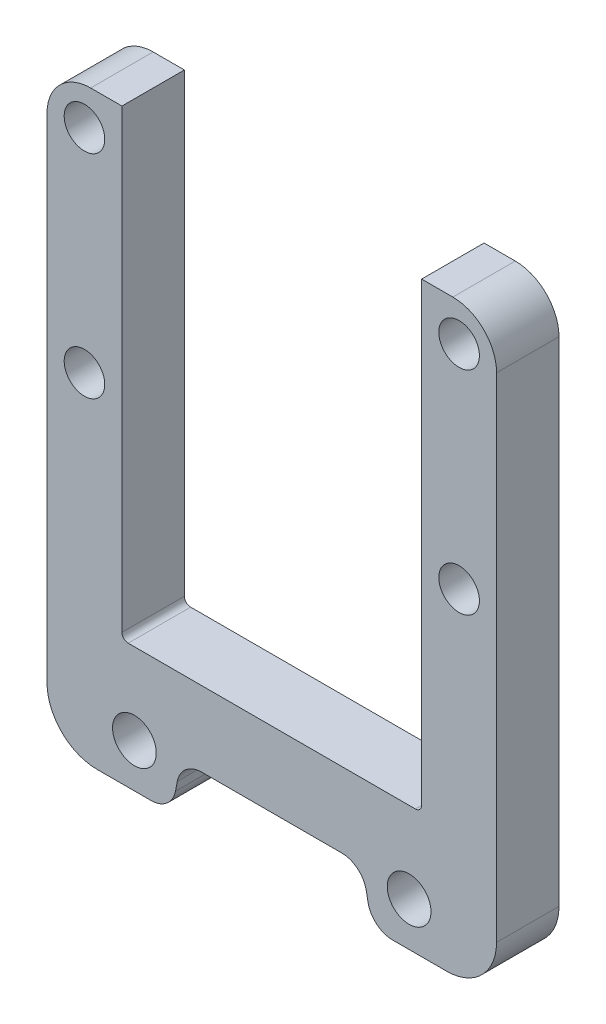
SolidWorks part; units mm, degrees
ref_plane "Plan de face" through (0, 0, 0) normal (0, 0, 1) x (1, 0, 0)
ref_plane "Plan de dessus" through (0, 0, 0) normal (0, 1, 0) x (1, 0, 0)
ref_plane "Plan de droite" through (0, 0, 0) normal (1, 0, 0) x (0, 0, -1)
sketch "Esquisse1" plane through (0, 0, 0) normal (0, 0, 1) x (1, 0, 0)
  line L0 (24, 110) -> (24, 36)
  line L1 (24, 36) -> (0, 36)
  line L7 (0, 24) -> (14.5, 24)
  line L8 (14.5, 24) -> (16.055, 16)
  line L9 (16.055, 16) -> (36, 16)
  line L10 (36, 16) -> (36, 110)
  line L11 (36, 110) -> (24, 110)
  line L12 (0, 36) -> (0, 24)
  line L13 (0, -0.15) -> (0, 72.4519) construction
  circle A0 centre (30, 104) radius 3.25
  circle A1 centre (22, 23) radius 3.5
  circle A3 centre (30, 70) radius 3.25
  point P19 (30, 110)
  dimension "D9" = 7
  dimension "D10" = 6
  dimension "D14" = 6.5
  dimension "D1" = 12
  dimension "D2" = 24
  dimension "D3" = 101
  dimension "D4" = 24
  dimension "D5" = 12
  dimension "D6" = 74
  dimension "D7" = 8
  dimension "D8" = 14.5
  dimension "D11" = 34
  dimension "D12" = 1
  dimension "D13" = 22
extrude "Boss.-Extru.1" add sketch "Esquisse1" along normal blind 10
mirror "Symétrie2" about plane through (0, 36, 10) normal (1, 0, 0) of "Boss.-Extru.1"
fillet "Congé1" radius 4 4 edges at (16.055, 16, 5) (-16.055, 16, 5) (-14.5, 24, 5) (14.5, 24, 5)
fillet "Congé2" radius 8 2 edges at (-36, 16, 5) (36, 16, 5)
fillet "Congé3" radius 7 2 edges at (36, 110, 5) (-36, 110, 5)
fillet "Congé4" radius 1 2 edges at (-24, 36, 5) (24, 36, 5)
